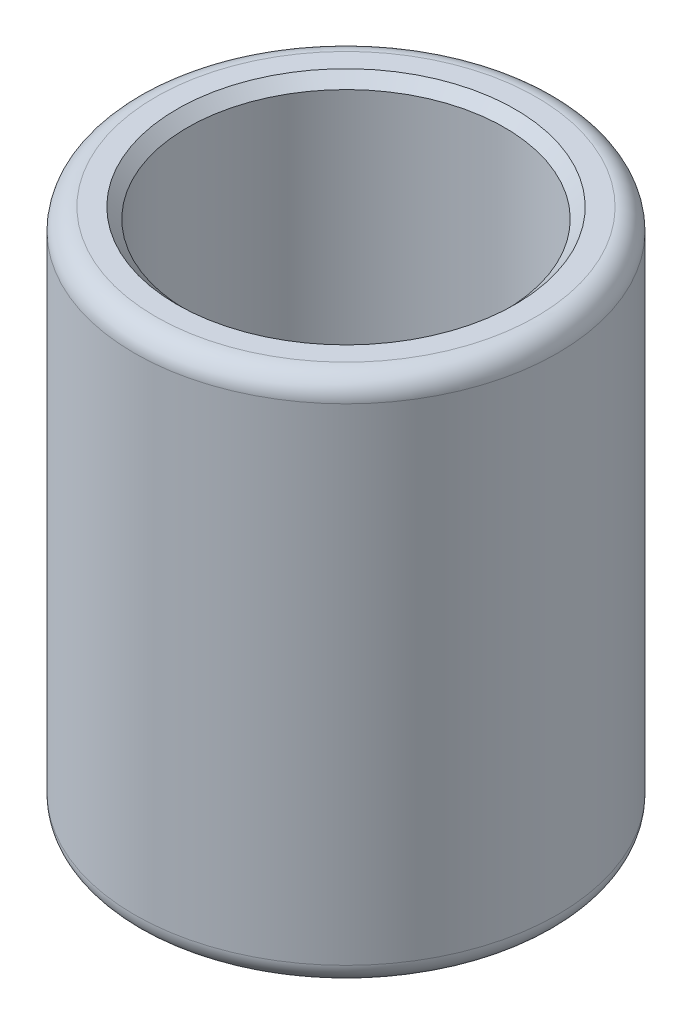
SolidWorks part; units mm, degrees
material "Liga de aço"
ref_plane "Plano frontal" through (0, 0, 0) normal (0, 0, 1) x (1, 0, 0)
ref_plane "Plano superior" through (0, 0, 0) normal (0, 1, 0) x (1, 0, 0)
ref_plane "Plano direito" through (0, 0, 0) normal (1, 0, 0) x (0, 0, -1)
sketch "Esboço1" plane through (0, 0, 0) normal (0, 1, 0) x (1, 0, 0)
  circle A0 centre (0, 0) radius 15
  circle A1 centre (0, 0) radius 20
  dimension "D1" = 30
  dimension "D2" = 40
extrude "Ressalto-extrusão1" add sketch "Esboço1" along normal blind 50
fillet "Filete1" radius 2 2 edges at (0, 0, 20) (0, 50, 20)
chamfer "Chanfro1" distance 1 angle 45 2 edges at (0, 0, 15) (0, 50, 15)
